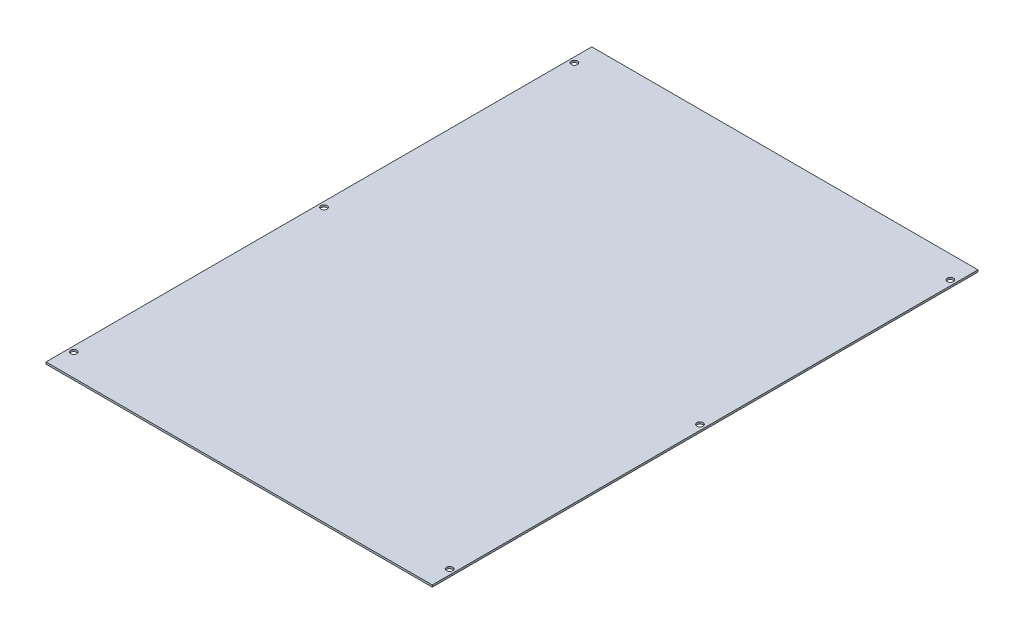
SolidWorks part; units mm, degrees
material "6061-T6 (SS)"
ref_plane "Front Plane" through (0, 0, 0) normal (0, 0, 1) x (1, 0, 0)
ref_plane "Top Plane" through (0, 0, 0) normal (0, 1, 0) x (1, 0, 0)
ref_plane "Right Plane" through (0, 0, 0) normal (1, 0, 0) x (0, 0, -1)
sketch "Sketch1" plane through (0, 0, 0) normal (0, 1, 0) x (1, 0, 0)
  line L0 (0, 0) -> (16.6802, 0) construction
  line L1 (-159.25, -225) -> (159.25, -225)
  line L2 (-159.25, -225) -> (-159.25, 225)
  line L3 (-159.25, 225) -> (159.25, 225)
  line L4 (159.25, -225) -> (159.25, 225)
  line L5 (-159.25, -225) -> (159.25, 225) construction
  line L6 (-159.25, 225) -> (159.25, -225) construction
  line L7 (0, 0) -> (0, 31.1117) construction
  line L9 (-155, -206.45) -> (155, -206.45) construction
  line L10 (-155, -206.45) -> (-155, 206.45) construction
  line L11 (-155, 206.45) -> (155, 206.45) construction
  line L12 (155, -206.45) -> (155, 206.45) construction
  line L13 (-155, -206.45) -> (155, 206.45) construction
  line L14 (-155, 206.45) -> (155, -206.45) construction
  point P0 (0, 0)
  point P13 (155, 0)
  point P14 (-155, 0)
  dimension "D1" = 318.5
  dimension "D2" = 450
  dimension "D3" = 412.9
  dimension "D4" = 310
extrude "Boss-Extrude1" add sketch "Sketch1" along normal blind 1.6002
hole_wizard "#10 Clearance Hole1" positions "Sketch3" profile "Sketch2" hole size "#10" standard "ANSI Inch"
sketch "Sketch3" plane through (0, 1.6002, 0) normal (0, 1, 0) x (1, 0, 0)
  point P0 (-155, 206.45)
  point P3 (155, 206.45)
  point P6 (155, 0)
  point P9 (155, -206.45)
  point P12 (-155, -206.45)
  point P15 (-155, 0)
sketch "Sketch2" plane through (-155, 1.6002, -206.45) normal (1, 0, 0) x (0, 0, 1)
  line L0 (0, 0) -> (0, 131.0638)
  line L1 (0, 131.0638) -> (2.5527, 129.53)
  line L2 (2.5527, 129.53) -> (2.5527, 0)
  line L5 (2.5527, 0) -> (0, 0)
  line L10 (0, 131.0638) -> (-2.5527, 129.53) construction
  line L11 (0, -6.35) -> (0, 107.95) construction
  dimension "Hole Dia." = 5.1054
  dimension "Hole Depth" = 129.53
  dimension "Drill Angle" = 118
